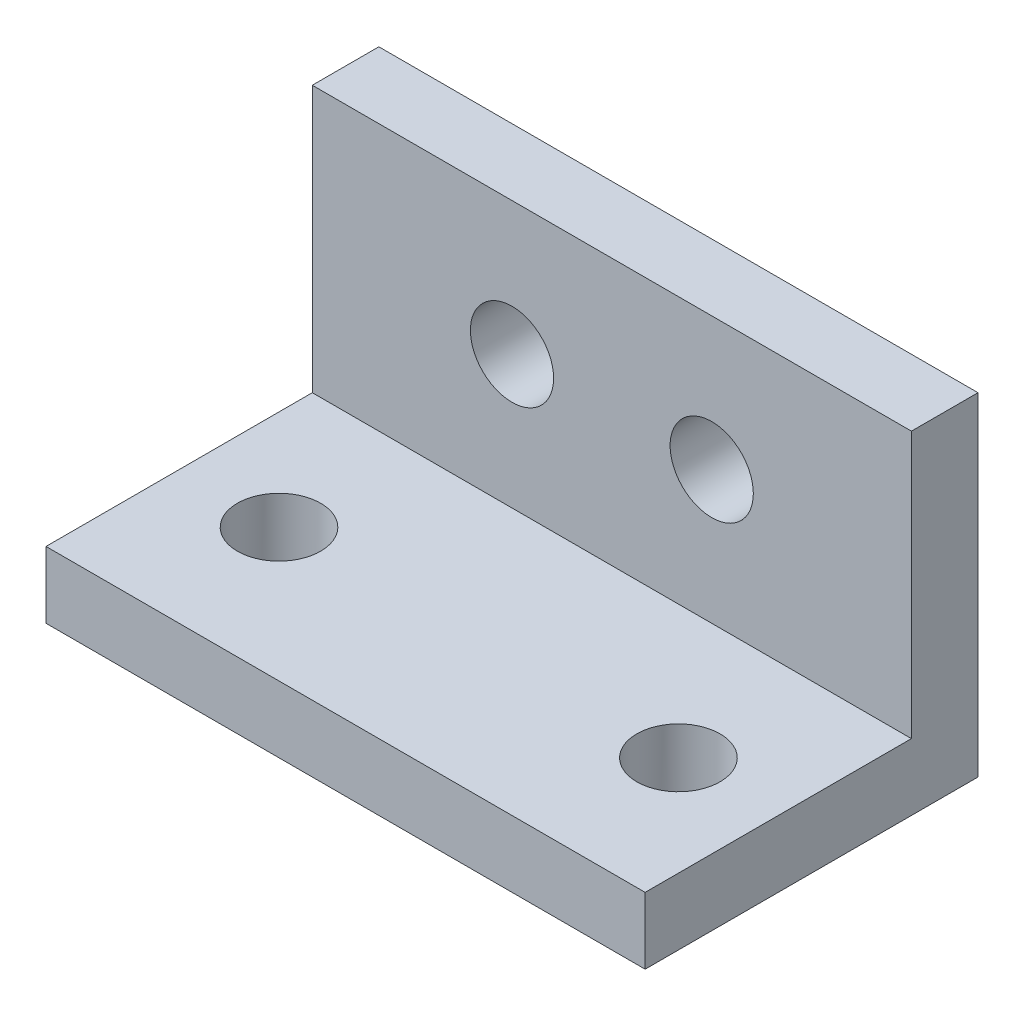
SolidWorks part; units mm, degrees
ref_plane "Front Plane" through (0, 0, 0) normal (0, 0, 1) x (1, 0, 0)
ref_plane "Top Plane" through (0, 0, 0) normal (0, 1, 0) x (1, 0, 0)
ref_plane "Right Plane" through (0, 0, 0) normal (1, 0, 0) x (0, 0, -1)
sketch "Sketch1" plane through (0, 0, 0) normal (1, 0, 0) x (0, 0, -1)
  line L1 (0, 0) -> (-6.35, 0)
  line L2 (0, 0) -> (0, 31.75)
  line L3 (0, 31.75) -> (-6.35, 31.75)
  line L4 (-6.35, 0) -> (-6.35, 31.75)
  line L5 (-6.35, 0) -> (-31.75, 0)
  line L6 (-6.35, 0) -> (-6.35, 6.35)
  line L7 (-6.35, 6.35) -> (-31.75, 6.35)
  line L8 (-31.75, 0) -> (-31.75, 6.35)
  dimension "D1" = 6.35
  dimension "D2" = 6.35
  dimension "D3" = 31.75
  dimension "D4" = 31.75
extrude "Boss-Extrude1" add sketch "Sketch1" along normal blind 57.15 contours L8 L5 L4 L7 | L4 L1 L2 L3
sketch "Sketch2" plane through (0, 0, 6.35) normal (0, 0, 1) x (1, 0, 0)
  line L0 (0, 19.05) -> (57.15, 19.05) construction
  line L1 (0, 6.35) -> (0, 31.75) construction
  line L2 (57.15, 6.35) -> (57.15, 31.75) construction
  line L3 (57.15, 6.35) -> (0, 6.35) construction
  circle A0 centre (19.05, 19.05) radius 3.9687
  circle A1 centre (38.1, 19.05) radius 3.9687
  dimension "D1" = 7.9375
  dimension "D4" = 7.9375
  dimension "D2" = 12.7
  dimension "D3" = 19.05
  dimension "D5" = 19.05
extrude "Cut-Extrude1" cut sketch "Sketch2" against normal up to next
sketch "Sketch3" plane through (0, 6.35, 0) normal (0, 1, 0) x (1, 0, 0)
  line L0 (0, -19.05) -> (57.15, -19.05) construction
  line L1 (0, -6.35) -> (0, -31.75) construction
  line L2 (57.15, -6.35) -> (57.15, -31.75) construction
  line L3 (57.15, -31.75) -> (57.15, -6.35) construction
  circle A0 centre (9.525, -19.05) radius 3.9688
  circle A1 centre (47.625, -19.05) radius 3.9687
  dimension "D1" = 7.9375
  dimension "D2" = 7.9375
  dimension "D3" = 9.525
  dimension "D4" = 9.525
extrude "Cut-Extrude2" cut sketch "Sketch3" against normal up to next
